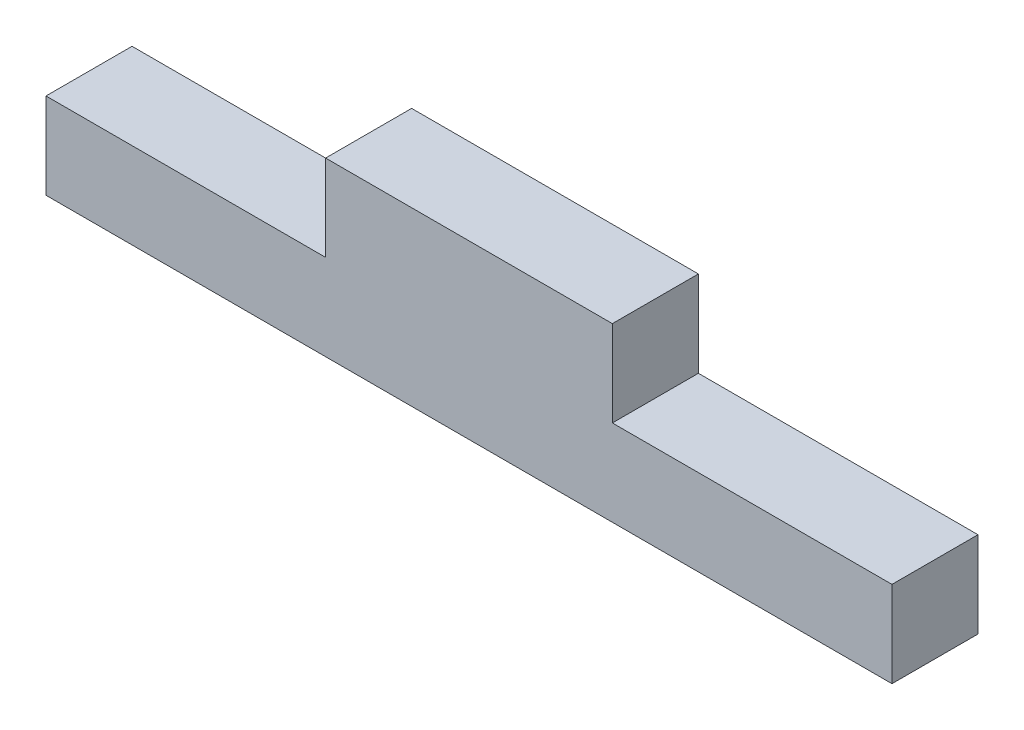
SolidWorks part; units mm, degrees
ref_plane "Plano frontal" through (0, 0, 0) normal (0, 0, 1) x (1, 0, 0)
ref_plane "Plano superior" through (0, 0, 0) normal (0, 1, 0) x (1, 0, 0)
ref_plane "Plano direito" through (0, 0, 0) normal (1, 0, 0) x (0, 0, -1)
sketch "Esboço1" plane through (0, 0, 0) normal (0, 0, 1) x (1, 0, 0)
  line L0 (19.5, 6) -> (19.5, 12)
  line L1 (0, 0) -> (59, 0)
  line L2 (0, 0) -> (0, 12)
  line L3 (0, 12) -> (59, 12)
  line L4 (59, 0) -> (59, 12)
  line L5 (0, 12) -> (6, 12)
  line L6 (0, 12) -> (0, 6)
  line L7 (0, 6) -> (19.5, 6)
  line L9 (59, 12) -> (53, 12)
  line L10 (59, 12) -> (59, 6)
  line L11 (59, 6) -> (39.5, 6)
  line L13 (39.5, 6) -> (39.5, 12)
  dimension "D1" = 12
  dimension "D2" = 59
  dimension "D3" = 6
  dimension "D4" = 19.5
  dimension "D5" = 19.5
extrude "Ressalto-extrusão1" add sketch "Esboço1" along normal blind 6
